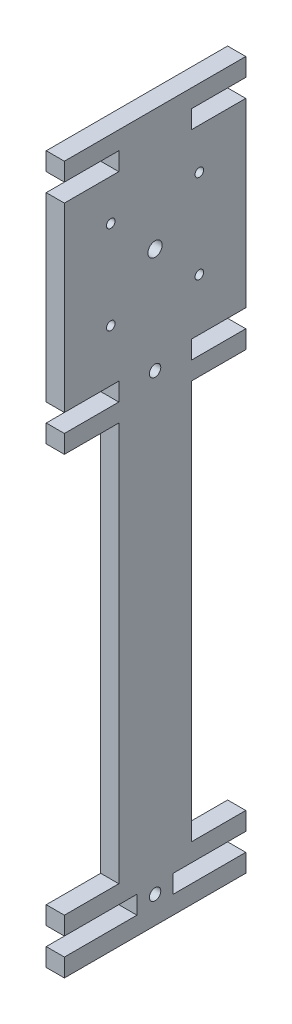
SolidWorks part; units mm, degrees
ref_plane "Front Plane" through (0, 0, 0) normal (0, 0, 1) x (1, 0, 0)
ref_plane "Top Plane" through (0, 0, 0) normal (0, 1, 0) x (1, 0, 0)
ref_plane "Right Plane" through (0, 0, 0) normal (1, 0, 0) x (0, 0, -1)
sketch "Sketch1" plane through (0, 0, 0) normal (1, 0, 0) x (0, 0, -1)
  line L0 (63.5, 184.15) -> (63.5, 215.9)
  line L1 (0, 25.4) -> (0, 177.8)
  line L2 (0, 12.7) -> (0, 19.05)
  line L4 (63.5, 12.7) -> (63.5, 19.05)
  line L5 (0, 228.6) -> (0, 254)
  line L6 (0, 19.05) -> (19.05, 19.05)
  line L7 (0, 228.6) -> (0, 215.9)
  line L8 (0, 25.4) -> (19.05, 25.4)
  line L9 (19.05, 19.05) -> (19.05, 25.4)
  line L10 (44.45, 25.4) -> (57.15, 25.4)
  line L11 (44.45, 25.4) -> (44.45, 19.05)
  line L12 (44.45, 19.05) -> (57.15, 19.05)
  line L13 (0, 12.7) -> (61.8679, 12.7)
  line L14 (0, 184.15) -> (19.05, 184.15)
  line L15 (63.5, 228.6) -> (63.5, 215.9)
  line L16 (0, 177.8) -> (19.05, 177.8)
  line L17 (19.05, 184.15) -> (19.05, 177.8)
  line L18 (44.45, 184.15) -> (63.5, 184.15)
  line L19 (44.45, 184.15) -> (44.45, 177.8)
  line L20 (44.45, 177.8) -> (63.5, 177.8)
  line L22 (61.8679, 12.7) -> (63.5, 12.7)
  line L23 (0, 184.15) -> (0, 215.9)
  line L25 (0, 254) -> (0, 260.35)
  line L26 (0, 260.35) -> (63.5, 260.35)
  line L27 (57.15, 19.05) -> (63.5, 19.05)
  line L28 (63.5, 254) -> (63.5, 260.35)
  line L30 (63.5, 228.6) -> (63.5, 254)
  line L31 (57.15, 25.4) -> (63.5, 25.4)
  line L32 (63.5, 25.4) -> (63.5, 177.8)
  circle A0 centre (31.75, 180.975) radius 2
  circle A1 centre (31.75, 22.225) radius 2
  dimension "D17" = 4
  dimension "D19" = 4
  dimension "D3" = 6.35
  dimension "D4" = 6.35
  dimension "D6" = 19.05
  dimension "D7" = 25.4
  dimension "D8" = 12.7
  dimension "D10" = 6.35
  dimension "D11" = 152.4
  dimension "D12" = 152.4
  dimension "D13" = 6.35
  dimension "D14" = 6.35
  dimension "D15" = 19.05
  dimension "D16" = 19.05
  dimension "D18" = 12.7
  dimension "D20" = 12.7
extrude "Boss-Extrude1" add sketch "Sketch1" along normal blind 6.35
sketch "Sketch2" plane through (6.35, 0, 0) normal (1, 0, 0) x (0, 0, -1)
  line L0 (63.5, 184.15) -> (44.45, 184.15) construction
  line L1 (10.75, 238.85) -> (52.75, 238.85) construction
  line L2 (10.75, 238.85) -> (10.75, 196.85) construction
  line L3 (10.75, 196.85) -> (52.75, 196.85) construction
  line L4 (52.75, 238.85) -> (52.75, 196.85) construction
  line L5 (10.75, 238.85) -> (52.75, 196.85) construction
  line L6 (10.75, 196.85) -> (52.75, 238.85) construction
  circle A0 centre (31.75, 180.975) radius 2 construction
  circle A1 centre (47.25, 233.35) radius 1.5
  circle A2 centre (31.75, 217.85) radius 2.5
  circle A3 centre (47.25, 202.35) radius 1.5
  circle A4 centre (16.25, 202.35) radius 1.5
  circle A5 centre (16.25, 233.35) radius 1.5
  point P0 (31.75, 217.85)
  point P25 (31.75, 217.85)
  dimension "D3" = 42
  dimension "D4" = 0
  dimension "D7" = 5.5
  dimension "D6" = 3
  dimension "D8" = 5
  dimension "D1" = 4
  dimension "D2" = 42
  dimension "D5" = 12.7
sketch "Sketch3" plane through (6.35, 0, 0) normal (1, 0, 0) x (0, 0, -1)
  line L0 (0, 177.8) -> (0, 25.4) construction
  line L1 (0, 171.45) -> (19.05, 171.45)
  line L2 (0, 171.45) -> (0, 31.75)
  line L3 (0, 31.75) -> (19.05, 31.75)
  line L4 (19.05, 171.45) -> (19.05, 31.75)
  line L5 (44.45, 171.45) -> (63.5, 171.45)
  line L6 (44.45, 171.45) -> (44.45, 31.75)
  line L7 (44.45, 31.75) -> (63.5, 31.75)
  line L8 (63.5, 171.45) -> (63.5, 31.75)
  line L9 (0, 25.4) -> (19.05, 25.4) construction
  line L10 (63.5, 184.15) -> (63.5, 260.35) construction
  line L11 (44.45, 25.4) -> (63.5, 25.4) construction
  dimension "D1" = 139.7
  dimension "D2" = 0
  dimension "D3" = 6.35
  dimension "D4" = 19.05
  dimension "D5" = 19.05
  dimension "D6" = 0
  dimension "D7" = 139.7
  dimension "D8" = 6.35
extrude "Cut-Extrude2" cut sketch "Sketch3" against normal blind 6.35
extrude "Cut-Extrude3" cut sketch "Sketch2" against normal blind 6.35
sketch "Sketch4" plane through (6.35, 0, 0) normal (1, 0, 0) x (0, 0, -1)
  line L1 (19.05, 25.4) -> (25.4, 25.4)
  line L2 (19.05, 25.4) -> (19.05, 19.05)
  line L3 (19.05, 19.05) -> (25.4, 19.05)
  line L4 (25.4, 25.4) -> (25.4, 19.05)
  line L5 (44.45, 25.4) -> (38.1, 25.4)
  line L6 (44.45, 25.4) -> (44.45, 19.05)
  line L7 (44.45, 19.05) -> (38.1, 19.05)
  line L8 (38.1, 25.4) -> (38.1, 19.05)
  circle A0 centre (31.75, 22.225) radius 2 construction
  dimension "D1" = 12.7
  dimension "D2" = 6.35
extrude "Cut-Extrude4" cut sketch "Sketch4" against normal blind 6.35
sketch "Sketch5" plane through (6.35, 0, 0) normal (1, 0, 0) x (0, 0, -1)
  line L0 (0, 260.35) -> (0, 184.15) construction
  line L1 (0, 254) -> (19.05, 254)
  line L2 (0, 254) -> (0, 247.65)
  line L3 (0, 247.65) -> (19.05, 247.65)
  line L4 (19.05, 254) -> (19.05, 247.65)
  line L5 (63.5, 184.15) -> (63.5, 260.35) construction
  line L6 (44.45, 254) -> (63.5, 254)
  line L7 (44.45, 254) -> (44.45, 247.65)
  line L8 (44.45, 247.65) -> (63.5, 247.65)
  line L9 (63.5, 254) -> (63.5, 247.65)
  line L10 (0, 184.15) -> (19.05, 184.15) construction
  line L11 (44.45, 184.15) -> (63.5, 184.15) construction
  dimension "D1" = 6.35
  dimension "D2" = 6.35
  dimension "D3" = 63.5
  dimension "D4" = 63.5
extrude "Cut-Extrude5" cut sketch "Sketch5" against normal blind 6.35
